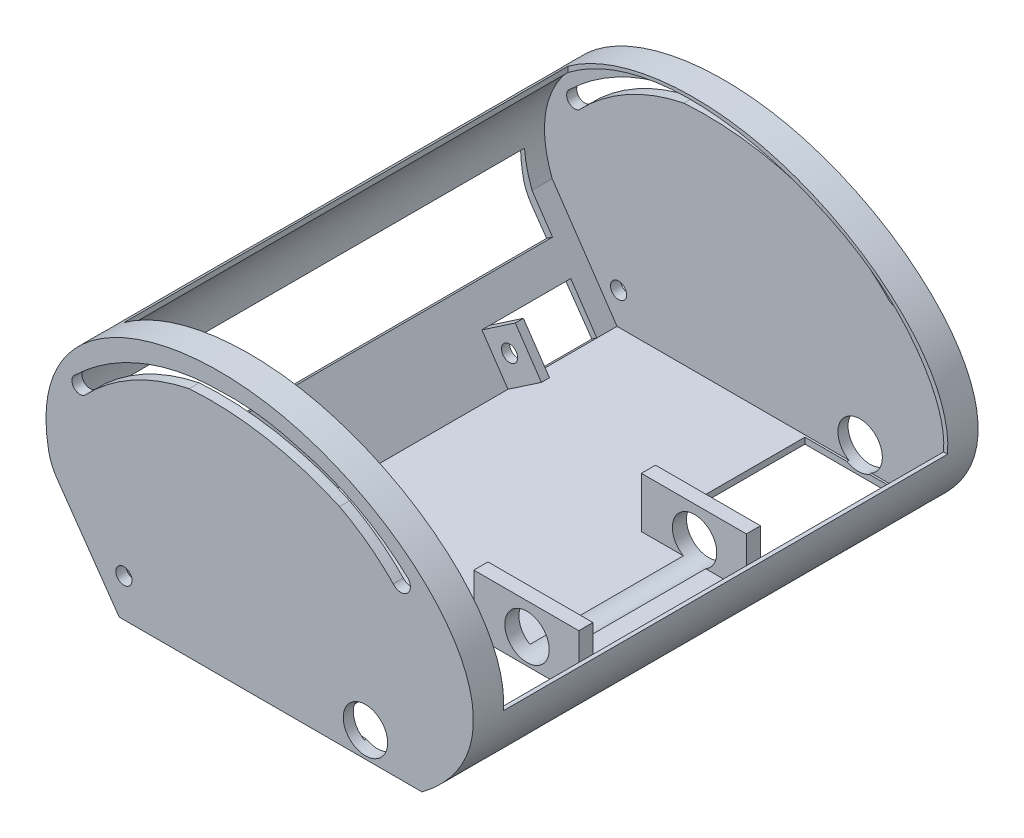
SolidWorks part; units mm, degrees
ref_plane "Front Plane" through (0, 0, 0) normal (0, 0, 1) x (1, 0, 0)
ref_plane "Top Plane" through (0, 0, 0) normal (0, 1, 0) x (1, 0, 0)
ref_plane "Right Plane" through (0, 0, 0) normal (1, 0, 0) x (0, 0, -1)
sketch "Sketch1" plane through (0, 0, 0) normal (0, 0, 1) x (1, 0, 0)
  line L0 (-74.4669, 0) -> (75.5331, 0)
  line L1 (-108.0812, 48.036) -> (-74.4669, 0)
  spline S0 degree 3 poles (75.5331, 0) (138.0634, 47.2005) (16.47, 172.0078) (-124.9496, 111.3016) (-108.0812, 48.036) knots 0 0 0 0 0.526875 1 1 1 1
  point P4 (-32.4145, 130)
  dimension "D1" = 150
  dimension "D2" = 130
extrude "Boss-Extrude1" add sketch "Sketch1" along normal blind 250
sketch "Sketch2" plane through (0, 0, 250) normal (0, 0, 1) x (1, 0, 0)
  line L0 (-105.0026, 50.2782) -> (-72.9037, 3)
  line L1 (-72.9037, 3) -> (73.1634, 3)
  line L2 (-74.4669, 0) -> (75.5331, 0) construction
  line L3 (-108.0812, 48.036) -> (-74.4669, 0) construction
  line L8 (73.1634, 3) -> (75.554, 3)
  line L9 (75.554, 3) -> (85.0551, 11.5917)
  arc A0 (85.0551, 11.5917) -> (92.7884, 23.0996) centre (54.7157, 40.3321) ccw
  spline S1 degree 3 poles (92.7884, 23.0996) (96.8127, 29.1542) (103.3148, 50.2014) (80.5015, 89.9804) (42.5402, 114.0057) (-11.8321, 131.7643) (-81.0967, 126.8199) (-117.2441, 82.1583) (-105.0026, 50.2782) knots 0.063094 0.063094 0.063094 0.063094 0.126753 0.268313 0.414747 0.542883 0.761533 1 1 1 1
  spline S2 degree 3 poles (75.5331, 0) (138.0634, 47.2005) (16.47, 172.0078) (-124.9496, 111.3016) (-108.0812, 48.036) knots 0 0 0 0 0.526875 1 1 1 1 construction
  point P0 (84.2255, 7.4524)
  point P14 (40.3797, 115.1008)
  point P15 (100.9394, 42.3743)
  point P16 (-27.9262, 130.1717)
  point P17 (-99.6443, 100.3852)
  point P18 (-110.6451, 63.8682)
  point P19 (-108.6451, 63.8682)
  point P20 (-106.521, 82.709)
  point P21 (-108.4645, 83.181)
  point P24 (-88.9532, 26.6391)
  point P26 (80.5084, 86.8702)
  point P31 (-28.0271, 128.5119)
  point P32 (-1.9168, 128.3747)
  point P33 (-75.5309, 119.4452)
  point P34 (-1.9168, 128.3747)
  point P39 (-108.0812, 48.036)
  dimension "D5" = 2
  dimension "D1" = 3
  dimension "D2" = 2
  dimension "D3" = 2
  dimension "D4" = 2
  dimension "D6" = 2
  dimension "D7" = 3.4043
  dimension "D9" = 2
  dimension "D10" = 2
  dimension "D11" = 2
  dimension "D12" = 3.8086
extrude "Cut-Extrude1" cut sketch "Sketch2" against normal blind 240 from offset 5 offset against normal yes
sketch "Sketch3" plane through (0, 0, 0) normal (0, 1, 0) x (1, 0, 0)
  line L0 (-87.293, -15) -> (-87.293, -235)
  line L1 (-87.293, -235) -> (100.952, -235)
  line L2 (100.952, -250) -> (100.952, 0) construction
  line L3 (100.952, -235) -> (100.952, -15)
  line L4 (100.952, -15) -> (-87.293, -15)
  line L5 (100.952, 0) -> (-110.7265, 0) construction
  line L6 (-110.7265, -250) -> (100.952, -250) construction
  dimension "D1" = 15
  dimension "D2" = 15
extrude "Cut-Extrude2" cut sketch "Sketch3" along normal blind 236 from offset 40
fillet "Fillet1" radius 25 1 edges at (-108.0812, 48.036, 125)
sketch "Sketch16" plane through (-48.5073, -32.9333, 0) normal (0.8273, 0.5617, 0) x (0, 0, -1)
  line L0 (-5, 43.4326) -> (-245, 43.4326) construction
  line L1 (-232.3287, 45.426) -> (-192.3287, 45.426)
  line L2 (-232.3287, 45.426) -> (-232.3287, 68.426)
  line L3 (-232.3287, 68.426) -> (-192.3287, 68.426)
  line L4 (-192.3287, 45.426) -> (-192.3287, 68.426)
  line L5 (-15, 43.4326) -> (-55, 43.4326)
  line L6 (-15, 43.4326) -> (-15, 66.4326)
  line L7 (-15, 66.4326) -> (-55, 66.4326)
  line L8 (-55, 43.4326) -> (-55, 66.4326)
  line L10 (-15, 142.0354) -> (-15, -23.5366) construction
  dimension "D1" = 23
  dimension "D2" = 40
  dimension "D3" = 23
  dimension "D4" = 40
extrude "Cut-Extrude11" cut sketch "Sketch16" against normal blind 170
sketch "Sketch17" plane through (-48.5073, -32.9333, 0) normal (0.8273, 0.5617, 0) x (0, 0, -1)
  line L0 (-55, 43.4326) -> (-245, 43.4326) construction
  line L1 (-192.3287, 68.426) -> (-188.3287, 68.426)
  line L2 (-192.3287, 68.426) -> (-192.3287, 43.4326)
  line L3 (-192.3287, 43.4326) -> (-188.3287, 43.4326)
  line L4 (-188.3287, 68.426) -> (-188.3287, 43.4326)
  line L7 (-55, 66.4326) -> (-59, 66.4326)
  line L8 (-55, 66.4326) -> (-55, 43.4326)
  line L9 (-55, 43.4326) -> (-59, 43.4326)
  line L10 (-59, 66.4326) -> (-59, 43.4326)
  dimension "D1" = 4
  dimension "D2" = 4
extrude "Boss-Extrude5" add sketch "Sketch17" along normal blind 20
sketch "Sketch18" plane through (0, 0, 55) normal (0, 0, -1) x (-1, 0, 0)
  circle A0 centre (72.1247, 18.8437) radius 4
  dimension "D1" = 8
extrude "Cut-Extrude12" cut sketch "Sketch18" against normal through all both and the other way through all
ref_plane "Plane1" through (0, 0, 125) normal (0, 0, 1) x (1, 0, 0)
sketch "Sketch26" plane through (0, 3, 0) normal (0, 1, 0) x (1, 0, 0)
  line L0 (-110.7265, 0) -> (-110.7265, -250) construction
  line L1 (21.1635, -244) -> (73.1635, -244)
  line L2 (21.1635, -244) -> (21.1635, -170)
  line L3 (21.1635, -170) -> (73.1635, -170)
  line L4 (73.1635, -244) -> (73.1635, -170)
  line L5 (-110.7265, -250) -> (100.952, -250) construction
  dimension "D1" = 131.89
  dimension "D2" = 52
  dimension "D3" = 74
  dimension "D4" = 6
extrude "Cut-Extrude13" cut sketch "Sketch26" against normal blind 10
sketch "Sketch27" plane through (0, 3, 0) normal (0, 1, 0) x (1, 0, 0)
  line L1 (21.1635, -170) -> (73.1635, -170)
  line L2 (21.1635, -170) -> (21.1635, -163)
  line L3 (21.1635, -163) -> (73.1635, -163)
  line L4 (73.1635, -170) -> (73.1635, -163)
  dimension "D1" = 7
extrude "Boss-Extrude6" add sketch "Sketch27" along normal blind 25
ref_plane "Plane2" through (0, 0, 125) normal (0, 0, 1) x (1, 0, 0)
mirror "Mirror1" about plane through (0, 0, 125) normal (0, 0, 1) of "Cut-Extrude13", "Boss-Extrude6"
sketch "Sketch29" plane through (0, 0, 87) normal (0, 0, 1) x (1, 0, 0)
  line L0 (-74.4669, 0) -> (75.5331, 0) construction
  line L1 (73.5021, 0) -> (21.5021, 0) construction
  line L2 (73.5021, 0) -> (73.5021, 25) construction
  line L3 (73.5021, 25) -> (21.5021, 25) construction
  line L4 (21.5021, 0) -> (21.5021, 25) construction
  circle A0 centre (47.5021, 12.5) radius 11
  point P4 (0, 0)
  point P10 (21.5021, 10.1081)
  dimension "D3" = 22
  dimension "D1" = 52
  dimension "D2" = 25
  dimension "D4" = 12.5
  dimension "D5" = 26
extrude "Cut-Extrude14" cut sketch "Sketch29" against normal through all both and the other way through all
sketch "Sketch31" plane through (-48.5073, -32.9333, 0) normal (0.8273, 0.5617, 0) x (0, 0, -1)
  line L0 (-235, -22.4129) -> (-235, 139.9002) construction
  line L1 (-235, 116.1151) -> (-15, 116.1151)
  line L2 (-235, 116.1151) -> (-235, 82.4774)
  line L3 (-235, 82.4774) -> (-15, 82.4774)
  line L4 (-15, 116.1151) -> (-15, 82.4774)
  line L5 (-15, 142.0354) -> (-15, -23.5366) construction
  point P8 (-235, 122.0952)
  point P9 (-235, 116.1151)
extrude "Cut-Extrude15" cut sketch "Sketch31" against normal through all both and the other way through all
sketch "Sketch33" plane through (0, 0, 250) normal (0, 0, 1) x (1, 0, 0)
  arc A0 (-96.1391, 93.0877) -> (-91.6362, 86.5096) centre (-93.8876, 89.7987) ccw
  arc A1 (-96.1391, 93.0877) -> (-24.5724, 121.9723) centre (-24.5724, 18.8704) cw
  arc A2 (68.7293, 88.0516) -> (14.1455, 117.1537) centre (-13.6663, -0.7498) ccw
  arc A3 (-24.5724, 121.9723) -> (14.1455, 117.1537) centre (-19.11, 7.9041) cw
  arc A4 (-91.6362, 86.5096) -> (-39.78, 115.3085) centre (-20.4241, 19.3695) cw
  arc A7 (34.6737, 101.9798) -> (-39.78, 115.3085) centre (-29.0392, -39.3059) ccw
  arc A8 (61.2487, 82.1621) -> (68.7293, 88.0516) centre (64.989, 85.1068) ccw
  arc A9 (61.2487, 82.1621) -> (34.6737, 101.9798) centre (-14.1212, 8.8202) ccw
extrude "Cut-Extrude17" cut sketch "Sketch33" against normal through all both
